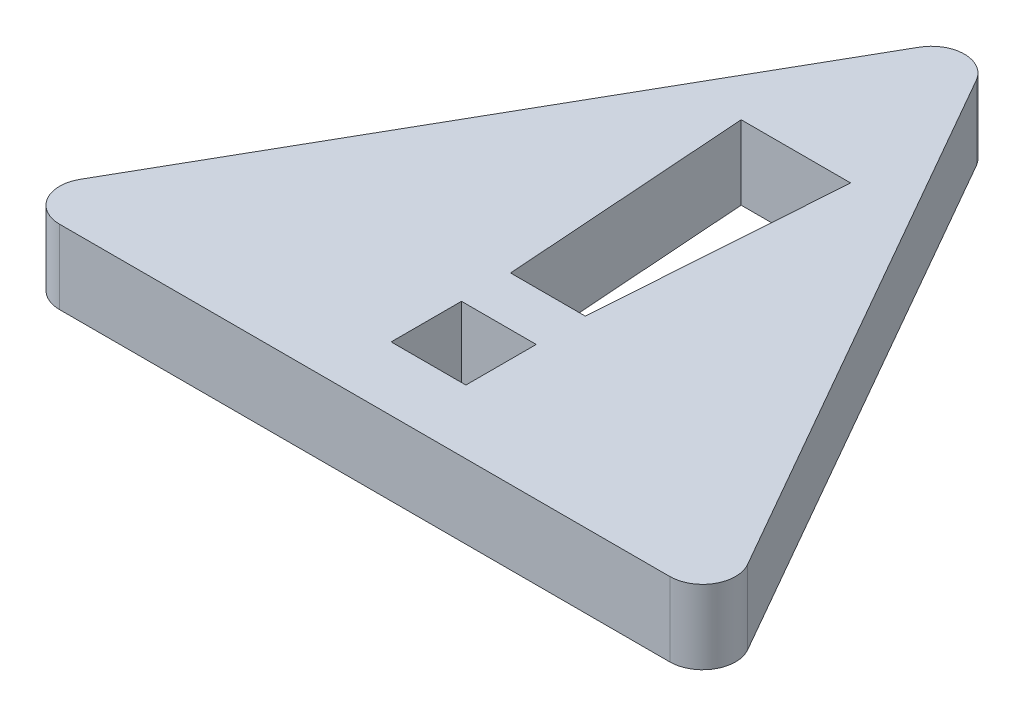
SolidWorks part; units mm, degrees
ref_plane "Front Plane" through (0, 0, 0) normal (0, 0, 1) x (1, 0, 0)
ref_plane "Top Plane" through (0, 0, 0) normal (0, 1, 0) x (1, 0, 0)
ref_plane "Right Plane" through (0, 0, 0) normal (1, 0, 0) x (0, 0, -1)
sketch "Sketch1" plane through (0, 0, 0) normal (0, 1, 0) x (1, 0, 0)
  line L0 (-17.1286, 1.8375) -> (-6.1286, 21.0875)
  line L1 (-6.1286, 21.0875) -> (4.8714, 1.8375)
  line L2 (4.8714, 1.8375) -> (-17.1286, 1.8375)
  line L3 (-7.2648, 7.4089) -> (-4.9924, 7.4089)
  line L4 (-7.2648, 5.9174) -> (-4.9924, 5.9174)
  line L5 (-7.2648, 5.9174) -> (-7.2648, 3.7787)
  line L6 (-7.2648, 3.7787) -> (-4.9924, 3.7787)
  line L7 (-4.9924, 5.9174) -> (-4.9924, 3.7787)
  line L8 (-4.9924, 7.4089) -> (-4.4639, 14.9495)
  line L9 (-7.2648, 7.4089) -> (-7.7932, 14.9495)
  line L10 (-7.7932, 14.9495) -> (-4.4639, 14.9495)
  point P9 (0, 0)
  dimension "D1" = 22
  dimension "D2" = 19.25
  dimension "D3" = 4.8714
  dimension "D4" = 4.4639
  dimension "D5" = 4.9924
  dimension "D6" = 7.2648
  dimension "D7" = 1.8375
  dimension "D8" = 3.7787
  dimension "D9" = 5.9174
  dimension "D10" = 7.4089
  dimension "D11" = 14.9495
extrude "Boss-Extrude1" add sketch "Sketch1" along normal blind 2.25
fillet "Fillet1" radius 1 3 edges at (-17.1286, 1.125, -1.8375) (4.8714, 1.125, -1.8375) (-6.1286, 1.125, -21.0875)
